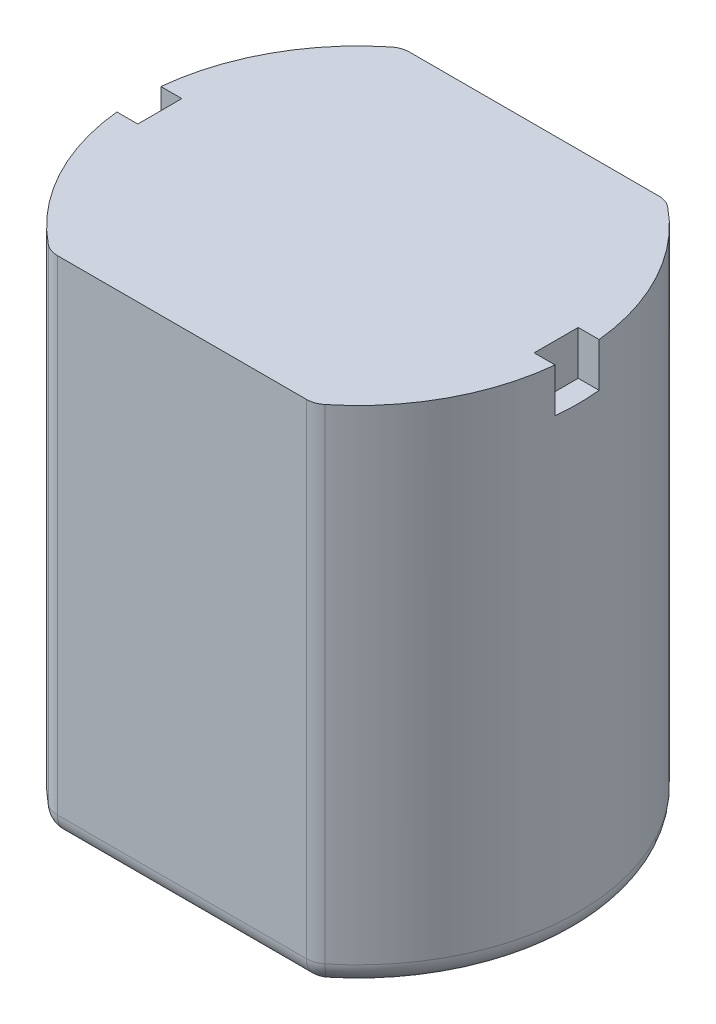
SolidWorks part; units mm, degrees
ref_plane "Front Plane" through (0, 0, 0) normal (0, 0, 1) x (1, 0, 0)
ref_plane "Top Plane" through (0, 0, 0) normal (0, 1, 0) x (1, 0, 0)
ref_plane "Right Plane" through (0, 0, 0) normal (1, 0, 0) x (0, 0, -1)
sketch "Sketch1" plane through (0, 0, 0) normal (0, 1, 0) x (1, 0, 0)
  line L0 (-3, 4) -> (3, 4)
  line L1 (-3.5034, 0) -> (8.8519, 0) construction
  line L2 (-3, -4) -> (3, -4)
  arc A0 (-3, 4) -> (-3, -4) centre (0, 0) ccw
  arc A1 (3, -4) -> (3, 4) centre (0, 0) ccw
  dimension "D1" = 10
  dimension "D2" = 4
extrude "Boss-Extrude1" add sketch "Sketch1" along normal blind 11.5 contours A0 L2 A1 L0
ref_plane "Plane1" through (5, 0, 0) normal (1, 0, 0) x (0, 0, -1)
sketch "Sketch3" plane through (5, 0, 0) normal (1, 0, 0) x (0, 0, -1)
  line L0 (4, 11.5) -> (-4, 11.5) construction
  line L1 (-0.5, 11.5) -> (0.5, 11.5)
  line L2 (-0.5, 11.5) -> (-0.5, 10.5)
  line L3 (-0.5, 10.5) -> (0.5, 10.5)
  line L4 (0.5, 11.5) -> (0.5, 10.5)
  line L5 (0, 0) -> (0, 12.4835) construction
  dimension "D1" = 1
  dimension "D2" = 0.5
  dimension "D3" = 1
extrude "Cut-Extrude1" cut sketch "Sketch3" against normal blind 0.5
mirror "Mirror1" about plane through (0, 0, 0) normal (1, 0, 0) of "Cut-Extrude1"
fillet "Fillet1" radius 0.5 4 edges at (-3, 5.75, -4) (3, 5.75, -4) (-3, 5.75, 4) (3, 5.75, 4)
fillet "Fillet2" radius 0.5 8 edges at (-2.9951, 0, 3.9714) (0, 0, 4) (2.9951, 0, 3.9714) (5, 0, 0) (2.9951, 0, -3.9714) (0, 0, -4) (-2.9951, 0, -3.9714) (-5, 0, 0)
sketch "Sketch4" plane through (0, 0, 0) normal (0, -1, 0) x (1, 0, 0)
  circle A0 centre (0, 0) radius 2
  dimension "D1" = 4
extrude "Boss-Extrude3" add sketch "Sketch4" along normal blind 0.25 contours A0
sketch "Sketch5" plane through (0, -0.25, 0) normal (0, -1, 0) x (1, 0, 0)
  circle A0 centre (0, 0) radius 0.25
  dimension "D1" = 0.5
extrude "Boss-Extrude4" add sketch "Sketch5" along normal blind 2.5
sketch "Sketch6" plane through (0, 0, 0) normal (0, -1, 0) x (1, 0, 0)
  circle A0 centre (-3, 0) radius 0.3763
  circle A1 centre (3, 0) radius 0.432
  dimension "D1" = 3
  dimension "D2" = 3
extrude "Cut-Extrude2" cut sketch "Sketch6" against normal blind 0.5
